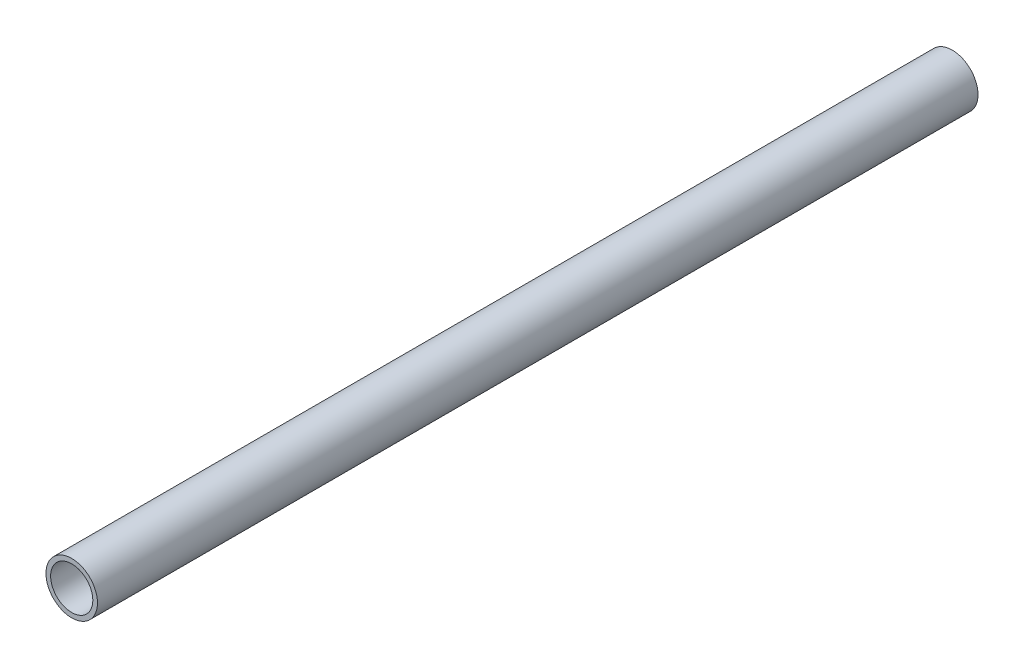
SolidWorks part; units mm, degrees
material "carbon"
ref_plane "Płaszczyzna XY" through (0, 0, 0) normal (0, 0, 1) x (1, 0, 0)
ref_plane "Płaszczyzna XZ" through (0, 0, 0) normal (0, 1, 0) x (1, 0, 0)
ref_plane "Płaszczyzna YZ" through (0, 0, 0) normal (1, 0, 0) x (0, 0, -1)
sketch "Szkic1" plane through (0, 0, 0) normal (0, 0, 1) x (1, 0, 0)
  circle A0 centre (0, 0) radius 6.35
  circle A1 centre (0, 0) radius 7.75
  dimension "D1" = 12.7
  dimension "D2" = 15.5
extrude "Dodanie-wyciągnięcie1" add sketch "Szkic1" along normal blind 219.7168 and the other way blind 45.2043
